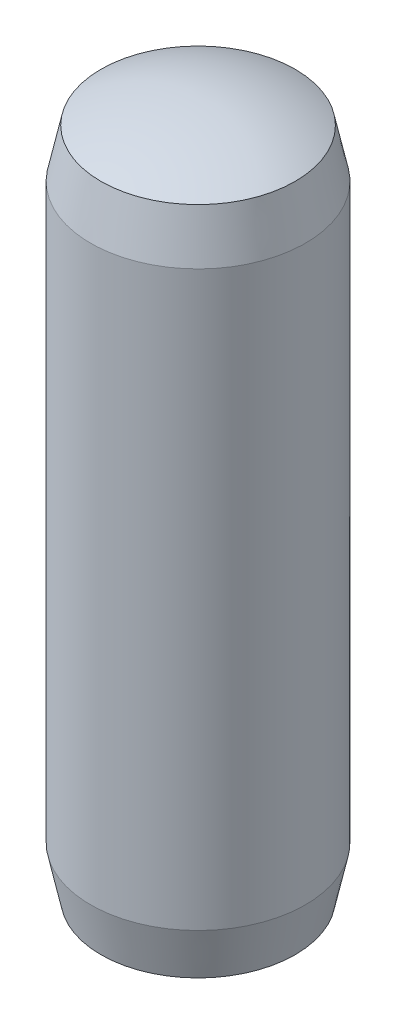
SolidWorks part; units mm, degrees
ref_plane "Front Plane" through (0, 0, 0) normal (0, 0, 1) x (1, 0, 0)
ref_plane "Top Plane" through (0, 0, 0) normal (0, 1, 0) x (1, 0, 0)
ref_plane "Right Plane" through (0, 0, 0) normal (1, 0, 0) x (0, 0, -1)
sketch "Sketch1" plane through (0, 0, 0) normal (0, 1, 0) x (1, 0, 0)
  circle A0 centre (0, 0) radius 0.75
  dimension "D1" = 1.5
extrude "Boss-Extrude1" add sketch "Sketch1" along normal blind 5
sketch "Sketch2" plane through (0, 0, 0) normal (0, 0, 1) x (1, 0, 0)
  line L0 (0, 0) -> (0, 5) construction
  line L1 (0.75, 5) -> (-0.75, 5) construction
  line L3 (0.75, 0) -> (0.75, 5) construction
  line L4 (0.75, 4.799) -> (0, 4.799) construction
  line L5 (0.75, 4.799) -> (0.75, 5.1)
  line L7 (0, 5) -> (0, 5.1)
  line L8 (0.75, 5.1) -> (-0.75, 5.1)
  line L9 (0.75, 5.1) -> (0, 5.1)
  line L10 (0, 2.5) -> (1.533, 2.5) construction
  line L11 (0.75, 0.201) -> (0, 0.201) construction
  line L12 (0.75, -0.1) -> (0, -0.1)
  line L13 (0, 0) -> (0, -0.1)
  line L14 (0.75, 0.201) -> (0.75, -0.1)
  arc A0 (0, 5) -> (0.75, 4.799) centre (0, 3.5) cw
  arc A1 (0, 0) -> (0.75, 0.201) centre (0, 1.5) ccw
  dimension "D1" = 1.5
  dimension "D2" = 0.1
revolve "Cut-Revolve2" cut sketch "Sketch2" angle 360 about L0
sketch "Sketch3" plane through (0, 0, 0) normal (0, 0, 1) x (1, 0, 0)
  line L0 (-0.75, 4.5) -> (-0.6782, 4.8379)
  line L1 (-0.75, 4.799) -> (-0.75, 0.201) construction
  line L2 (-0.75, 4.799) -> (-0.75, 4.5)
  line L3 (0, 0) -> (0, 5) construction
  line L4 (0, 2.5) -> (0.75, 2.5) construction
  line L5 (0.75, 0.201) -> (0.75, 4.799) construction
  line L6 (-0.75, 0.201) -> (-0.75, 0.5)
  line L7 (-0.75, 0.5) -> (-0.6782, 0.1621)
  arc A0 (0.75, 4.799) -> (-0.75, 4.799) centre (0, 3.5) ccw construction
  arc A1 (-0.6782, 4.8379) -> (-0.75, 4.799) centre (0, 3.5) ccw
  arc A2 (-0.6782, 0.1621) -> (-0.75, 0.201) centre (0, 1.5) cw
  dimension "D1" = 12
  dimension "D2" = 0.5
revolve "Cut-Revolve3" cut sketch "Sketch3" angle 360 about L3
